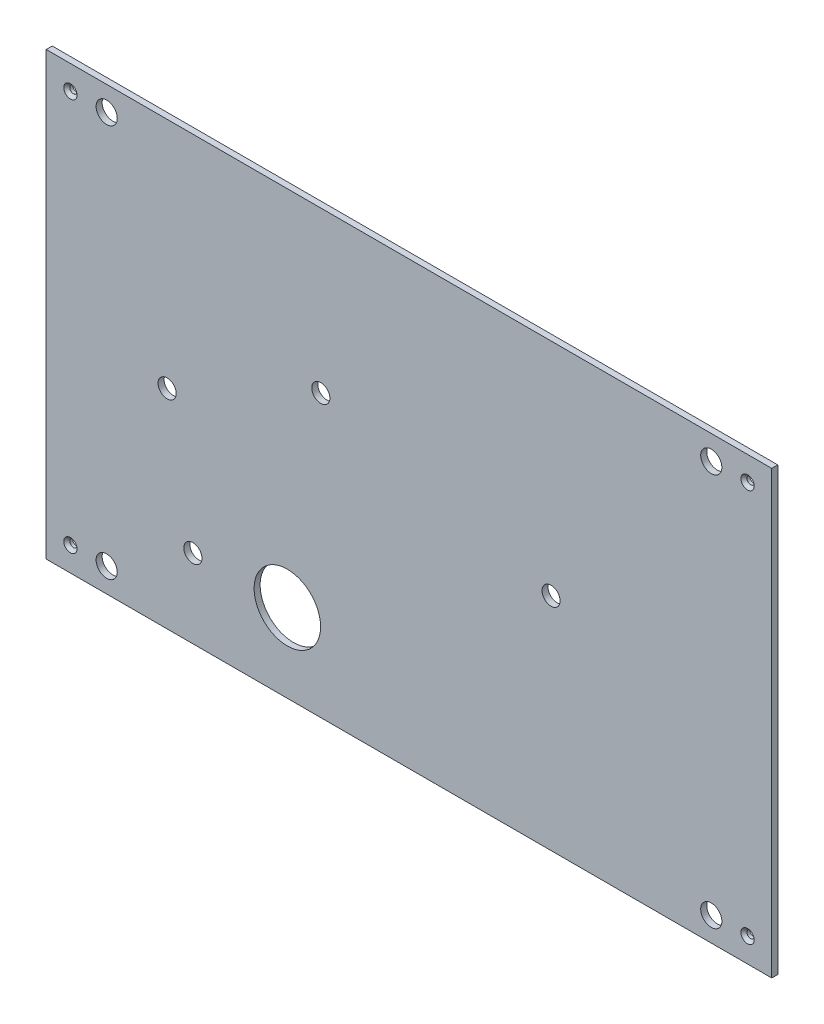
SolidWorks part; units mm, degrees
material "Сталь ШХ15 ГОСТ 801-78"
ref_plane "Plane1" through (0, 0, 0) normal (0, 0, 1) x (1, 0, 0)
ref_plane "Plane2" through (0, 0, 0) normal (0, 1, 0) x (1, 0, 0)
ref_plane "Plane3" through (0, 0, 0) normal (1, 0, 0) x (0, 0, -1)
sketch "Эскиз1" plane through (0, 0, 0) normal (0, 0, 1) x (1, 0, 0)
  line L1 (0, 0) -> (240, 0)
  line L2 (0, 0) -> (0, 146)
  line L3 (0, 146) -> (240, 146)
  line L4 (240, 0) -> (240, 146)
  line L5 (120, 146) -> (120, 0) construction
  line L6 (0, 73) -> (240, 73) construction
  circle A0 centre (79.7654, 26) radius 11
  circle A1 centre (48.5154, 26) radius 3
  circle A4 centre (167, 73) radius 3
  circle A5 centre (90.832, 93) radius 3
  circle A6 centre (40, 68.9133) radius 3
  circle A7 centre (20, 138) radius 3.5
  circle A8 centre (220, 138) radius 3.5
  circle A9 centre (220, 8) radius 3.5
  circle A10 centre (20, 8) radius 3.5
  circle A11 centre (8, 138) radius 2.5
  circle A12 centre (232, 138) radius 2.5
  circle A13 centre (232, 8) radius 2.5
  circle A14 centre (8, 8) radius 2.5
  point P35 (0, 0)
  dimension "D3" = 22
  dimension "D4" = 78.75
  dimension "D5" = 6
  dimension "D6" = 31.25
  dimension "D9" = 73
  dimension "D7" = 73
  dimension "D17" = 7
  dimension "D18" = 5
  dimension "D1" = 146
  dimension "D2" = 43.75
  dimension "D8" = 26
  dimension "D10" = 56.25
  dimension "D11" = 40
  dimension "D12" = 53
  dimension "D13" = 26
  dimension "D14" = 240
  dimension "D15" = 8
  dimension "D16" = 20
  dimension "D19" = 8
extrude "Бобышка-Вытянуть1" add sketch "Эскиз1" along normal blind 2
hole_wizard "Зенковка для винта с полупотайной головкой M22" positions "Эскиз6" profile "Эскиз7" countersink size "M2" standard "ISO" end condition through all
sketch "Эскиз6" plane through (0, 0, 2) normal (0, 0, 1) x (1, 0, 0)
  point P0 (8, 138)
  point P3 (232, 138)
  point P6 (232, 8)
  point P9 (8, 8)
sketch "Эскиз7" plane through (8, 138, 2) normal (1, 0, 0) x (0, -1, 0)
  line L0 (0, 0) -> (0, 2)
  line L1 (0, 2) -> (1.2, 2)
  line L2 (1.2, 2) -> (1.2, 1)
  line L3 (1.2, 1) -> (2.2, 0)
  line L5 (2.2, 0) -> (0, 0)
  line L6 (-1.2, 1) -> (-2.2, 0) construction
  line L11 (0, -6.35) -> (0, 107.95) construction
  dimension "Диаметр сквозного отверстия" = 2.4
  dimension "Глубина сквозного отверстия" = 2
  dimension "Диаметр передней зенковки" = 4.4
  dimension "Угол передней зенковки" = 90
